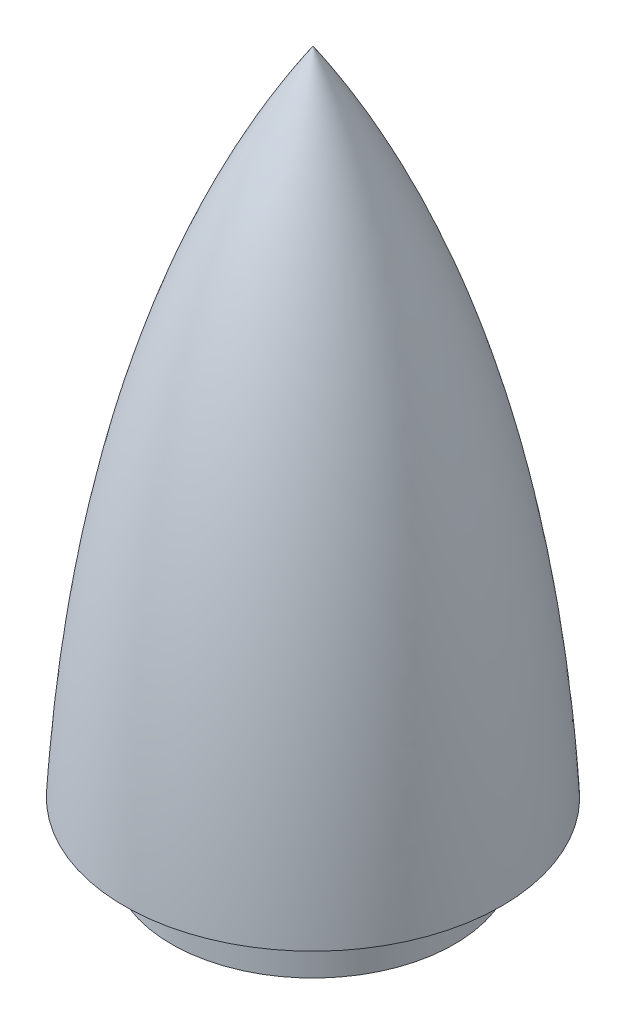
SolidWorks part; units mm, degrees
ref_plane "Front Plane" through (0, 0, 0) normal (0, 0, 1) x (1, 0, 0)
ref_plane "Top Plane" through (0, 0, 0) normal (0, 1, 0) x (1, 0, 0)
ref_plane "Right Plane" through (0, 0, 0) normal (1, 0, 0) x (0, 0, -1)
sketch "Sketch1" plane through (0, 0, 0) normal (0, 0, 1) x (1, 0, 0)
  line L0 (0, 74.9922) -> (0, -0.0078) construction
  line L1 (0, 74.9922) -> (0, -0.0078)
  line L3 (20, 5.9922) -> (15, 5.9922)
  line L4 (15, 5.9922) -> (15, -0.0078)
  line L5 (15, -0.0078) -> (0, -0.0078)
  spline S0 degree 2 poles (0, 74.9922) (17.6337, 48.5258) (20, 5.9922) knots 0 0 0 0.771738 0.771738 0.771738
  dimension "D1" = 15
  dimension "D2" = 6
  dimension "D3" = 75
  dimension "D4" = 20
revolve "Revolve1" add sketch "Sketch1" angle 360 about L0
